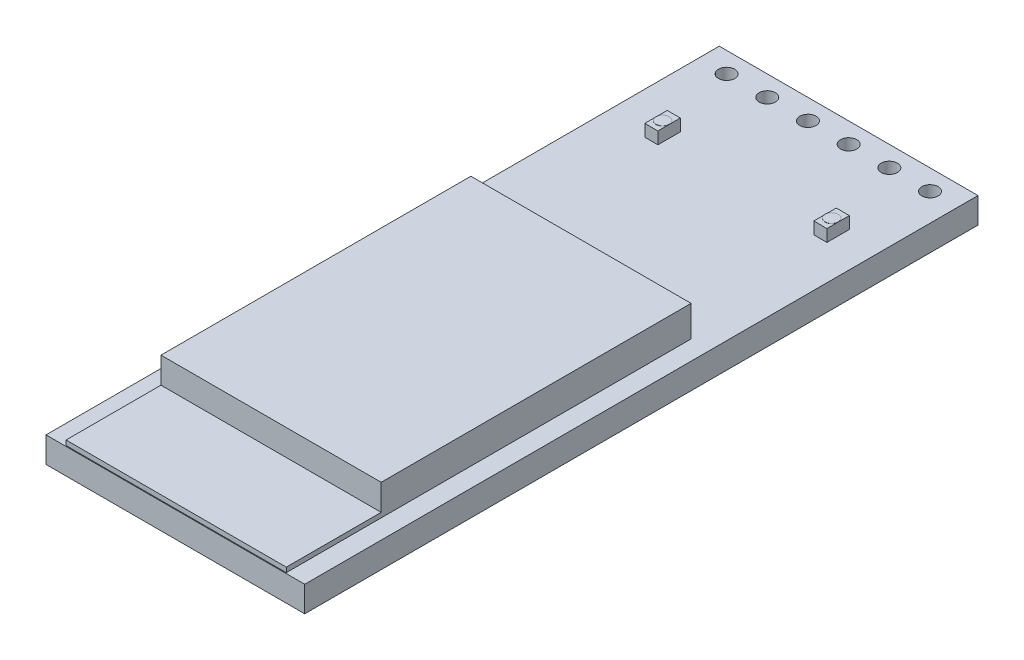
SolidWorks part; units mm, degrees
ref_plane "Front Plane" through (0, 0, 0) normal (0, 0, 1) x (1, 0, 0)
ref_plane "Top Plane" through (0, 0, 0) normal (0, 1, 0) x (1, 0, 0)
ref_plane "Right Plane" through (0, 0, 0) normal (1, 0, 0) x (0, 0, -1)
sketch "Sketch1" plane through (0, 0, 0) normal (0, 1, 0) x (1, 0, 0)
  line L0 (0, 0) -> (0, 97.247) construction
  line L1 (0, 0) -> (85.6465, 0) construction
  line L2 (-8.0772, 21.0185) -> (8.0772, 21.0185)
  line L3 (8.0772, 21.0185) -> (8.0772, -21.0185)
  line L4 (-8.0772, -21.0185) -> (8.0772, -21.0185)
  line L5 (-8.0772, 21.0185) -> (-8.0772, -21.0185)
  point P8 (8.0772, 0)
  point P10 (0, -21.0185)
  point P11 (0, 21.0185)
  dimension "D1" = 16.1544
  dimension "D2" = 42.037
extrude "Boss-Extrude1" add sketch "Sketch1" along normal mid plane 1.6002
sketch "Sketch2" plane through (0, 0.8001, 0) normal (0, 1, 0) x (1, 0, 0)
  line L0 (-8.0772, 19.7485) -> (8.0772, 19.7485) construction
  line L1 (-1.27, 19.7485) -> (-1.27, 20.2565) construction
  line L2 (-1.27, 20.2565) -> (1.27, 20.2565) construction
  line L3 (1.27, 20.2565) -> (1.27, 19.7485) construction
  line L4 (8.0772, -21.0185) -> (8.0772, 21.0185)
  line L5 (8.0772, 21.0185) -> (-8.0772, 21.0185)
  line L6 (-8.0772, 21.0185) -> (-8.0772, -21.0185)
  line L7 (-8.0772, -21.0185) -> (8.0772, -21.0185)
  line L8 (8.0772, -21.0185) -> (8.0772, 21.0185)
  line L9 (8.0772, 21.0185) -> (-8.0772, 21.0185)
  line L10 (-8.0772, 21.0185) -> (-8.0772, -21.0185)
  line L11 (-8.0772, -21.0185) -> (8.0772, -21.0185)
  line L12 (0, 20.2565) -> (0, 21.0185) construction
  circle A0 centre (-6.35, 19.7485) radius 0.508
  circle A1 centre (-3.81, 19.7485) radius 0.508
  circle A2 centre (-1.27, 19.7485) radius 0.508
  circle A3 centre (1.27, 19.7485) radius 0.508
  circle A4 centre (3.81, 19.7485) radius 0.508
  circle A5 centre (6.35, 19.7485) radius 0.508
  dimension "D7" = 1.016
  dimension "D2" = 2.54
  dimension "D3" = 2.54
  dimension "D4" = 2.54
  dimension "D5" = 2.54
  dimension "D6" = 2.54
  dimension "D8" = 1.27
  dimension "D1" = 0
extrude "Cut-Extrude1" cut sketch "Sketch2" against normal blind 1.6002 contours A0 | A1 | A2 | A3 | A4 | A5
sketch "Sketch3" plane through (0, 0.8001, 0) normal (0, 1, 0) x (1, 0, 0)
  line L0 (0, 0) -> (0, -21.0185) construction
  line L1 (-6.875, 4.3065) -> (6.875, 4.3065)
  line L2 (6.875, 4.3065) -> (6.875, -21.0185)
  line L3 (-6.875, 4.3065) -> (-6.875, -21.0185)
  line L4 (8.0772, -21.0185) -> (8.0772, 21.0185)
  line L5 (8.0772, 21.0185) -> (-8.0772, 21.0185)
  line L6 (-8.0772, 21.0185) -> (-8.0772, -21.0185)
  line L7 (-8.0772, -21.0185) -> (8.0772, -21.0185)
  line L8 (8.0772, -21.0185) -> (8.0772, 21.0185)
  line L9 (8.0772, 21.0185) -> (-8.0772, 21.0185)
  line L10 (-8.0772, 21.0185) -> (-8.0772, -21.0185)
  line L11 (-8.0772, -21.0185) -> (8.0772, -21.0185)
  line L12 (-6.875, -20.9685) -> (6.875, -20.9685)
  point P12 (0, 4.3065)
  dimension "D2" = 13.75
  dimension "D3" = 25.325
  dimension "D4" = 0.05
  dimension "D1" = 0
extrude "Boss-Extrude2" add sketch "Sketch3" along normal blind 0.3
sketch "Sketch4" plane through (0, 1.1001, 0) normal (0, 1, 0) x (1, 0, 0)
  line L0 (-6.875, -15.0435) -> (6.875, -15.0435)
  line L4 (-6.875, -20.9685) -> (6.875, -20.9685)
  line L5 (6.875, -20.9685) -> (6.875, 4.3065)
  line L6 (6.875, 4.3065) -> (-6.875, 4.3065)
  line L7 (-6.875, 4.3065) -> (-6.875, -20.9685)
  line L8 (-6.875, -20.9685) -> (6.875, -20.9685)
  line L9 (6.875, -20.9685) -> (6.875, 4.3065)
  line L10 (6.875, 4.3065) -> (-6.875, 4.3065)
  line L11 (-6.875, 4.3065) -> (-6.875, -20.9685)
  line M6 (6.875, -20.9685) -> (6.875, 4.3065)
  line M7 (6.875, 4.3065) -> (-6.875, 4.3065)
  line M8 (-6.875, 4.3065) -> (-6.875, -20.9685)
  dimension "D2" = 19.35
  dimension "D1" = 0
extrude "Boss-Extrude3" add sketch "Sketch4" along normal blind 1.625 contours L0 M8 M6 M7
sketch "Sketch5" plane through (0, 0.8001, 0) normal (0, 1, 0) x (1, 0, 0)
  line L1 (5.0772, 15.1685) -> (5.8972, 15.1685)
  line L2 (5.0772, 15.1685) -> (5.0772, 13.7685)
  line L3 (5.0772, 13.7685) -> (5.8972, 13.7685)
  line L4 (8.0772, -21.0185) -> (8.0772, 21.0185)
  line L5 (8.0772, 21.0185) -> (-8.0772, 21.0185)
  line L6 (-8.0772, 21.0185) -> (-8.0772, -21.0185)
  line L7 (-8.0772, -21.0185) -> (8.0772, -21.0185)
  line L8 (8.0772, -21.0185) -> (8.0772, 21.0185)
  line L9 (8.0772, 21.0185) -> (-8.0772, 21.0185)
  line L10 (-8.0772, 21.0185) -> (-8.0772, -21.0185)
  line L11 (-8.0772, -21.0185) -> (8.0772, -21.0185)
  line L12 (5.8972, 15.1685) -> (5.8972, 13.7685)
  line L13 (-5.4772, 15.1685) -> (-4.6572, 15.1685)
  line L14 (-5.4772, 15.1685) -> (-5.4772, 13.7685)
  line L15 (-5.4772, 13.7685) -> (-4.6572, 13.7685)
  line L16 (-4.6572, 15.1685) -> (-4.6572, 13.7685)
  dimension "D2" = 1.4
  dimension "D3" = 0.82
  dimension "D4" = 7.25
  dimension "D5" = 3
  dimension "D6" = 2.6
  dimension "D1" = 0
extrude "Boss-Extrude4" add sketch "Sketch5" along normal blind 0.75 contours L16 L13 L14 L15 | L12 L1 L2 L3
sketch "Sketch6" plane through (0, 1.5501, 0) normal (0, 1, 0) x (1, 0, 0)
  line L0 (-5.4772, 14.4685) -> (-4.6572, 14.4685) construction
  line L1 (-4.6572, 14.4685) -> (-5.0672, 15.1685) construction
  line L2 (-5.0672, 15.1685) -> (-5.0672, 13.7685) construction
  line L3 (5.4872, 15.1685) -> (5.4872, 13.7685) construction
  line L4 (-4.6572, 13.7685) -> (-4.6572, 15.1685)
  line L5 (-4.6572, 15.1685) -> (-5.4772, 15.1685)
  line L6 (-5.4772, 15.1685) -> (-5.4772, 13.7685)
  line L7 (-5.4772, 13.7685) -> (-4.6572, 13.7685)
  line L8 (-4.6572, 13.7685) -> (-4.6572, 15.1685)
  line L9 (-4.6572, 15.1685) -> (-5.4772, 15.1685)
  line L10 (-5.4772, 15.1685) -> (-5.4772, 13.7685)
  line L11 (-5.4772, 13.7685) -> (-4.6572, 13.7685)
  line L12 (5.4872, 13.7685) -> (5.0772, 14.4685) construction
  line L13 (5.0772, 14.4685) -> (5.8972, 14.4685) construction
  line L15 (5.8972, 13.7685) -> (5.8972, 15.1685)
  line L16 (5.8972, 15.1685) -> (5.0772, 15.1685)
  line L17 (5.0772, 15.1685) -> (5.0772, 13.7685)
  line L18 (5.0772, 13.7685) -> (5.8972, 13.7685)
  line L19 (5.8972, 13.7685) -> (5.8972, 15.1685)
  line L20 (5.8972, 15.1685) -> (5.0772, 15.1685)
  line L21 (5.0772, 15.1685) -> (5.0772, 13.7685)
  line L22 (5.0772, 13.7685) -> (5.8972, 13.7685)
  circle A0 centre (-5.0672, 14.4685) radius 0.41
  circle A1 centre (5.4872, 14.4685) radius 0.41
  dimension "D1" = 0
  dimension "D2" = 0
extrude "Boss-Extrude5" add sketch "Sketch6" along normal blind 0.01 contours A0 | A1
